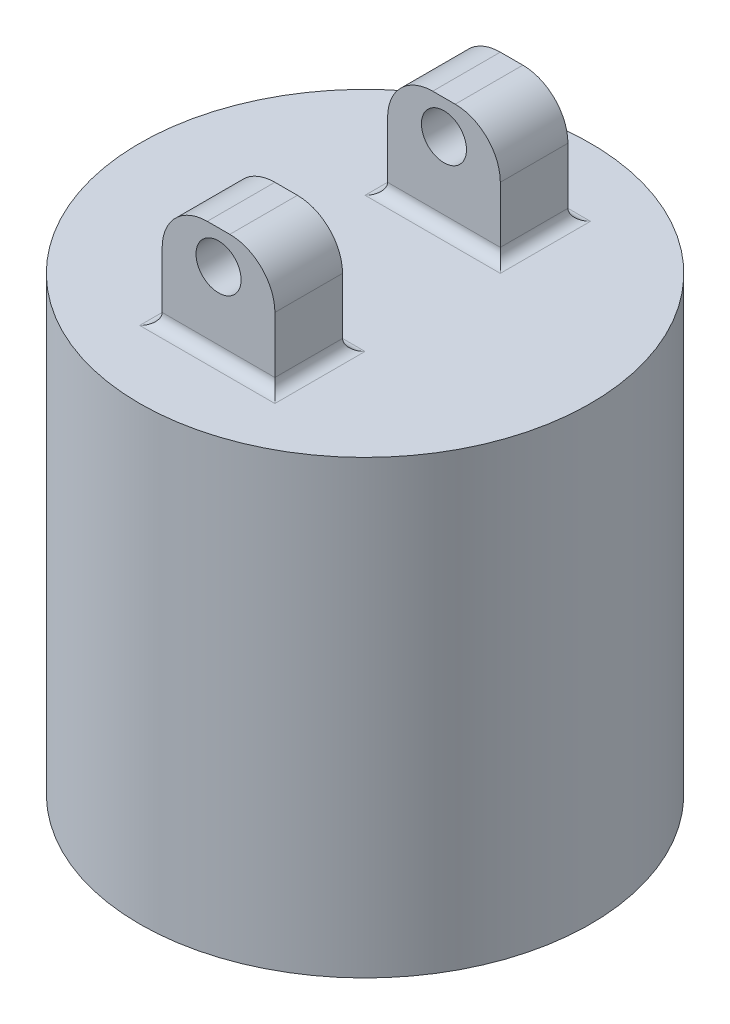
SolidWorks part; units mm, degrees
ref_plane "Front Plane" through (0, 0, 0) normal (0, 0, 1) x (1, 0, 0)
ref_plane "Top Plane" through (0, 0, 0) normal (0, 1, 0) x (1, 0, 0)
ref_plane "Right Plane" through (0, 0, 0) normal (1, 0, 0) x (0, 0, -1)
sketch "Sketch1" plane through (0, 0, 0) normal (0, 1, 0) x (1, 0, 0)
  circle A0 centre (0, 0) radius 50
  dimension "D1" = 100
extrude "Boss-Extrude1" add sketch "Sketch1" along normal blind 100
sketch "Sketch2" plane through (0, 100, 0) normal (0, 1, 0) x (1, 0, 0)
  line L1 (-12.5, -17.5) -> (12.5, -17.5)
  line L2 (-12.5, -17.5) -> (-12.5, -32.5)
  line L3 (-12.5, -32.5) -> (12.5, -32.5)
  line L4 (12.5, -17.5) -> (12.5, -32.5)
  line L5 (-12.5, -17.5) -> (12.5, -32.5) construction
  line L6 (-12.5, -32.5) -> (12.5, -17.5) construction
  point P0 (0, -25)
  point P5 (0, 0)
  point P7 (0, 0)
  point P8 (76.2365, 16.2508)
  dimension "D1" = 25
  dimension "D2" = 0
  dimension "D3" = 25
  dimension "D4" = 15
extrude "Boss-Extrude2" add sketch "Sketch2" along normal blind 25
fillet "Fillet1" radius 2.5 4 edges at (0, 100, 17.5) (-12.5, 100, 25) (0, 100, 32.5) (12.5, 100, 25)
fillet "Fillet2" radius 10 2 edges at (-12.5, 125, 25) (12.5, 125, 25)
sketch "Sketch3" plane through (0, 0, 32.5) normal (0, 0, 1) x (1, 0, 0)
  line L0 (-2.5, 125) -> (2.5, 125) construction
  line L3 (12.5, 115) -> (12.5, 102.5) construction
  circle A0 centre (0, 117.5) radius 5
  point P2 (-9.0351, 108.9927)
  point P5 (0, 125)
  point P6 (-3.9222, 117.5)
  point P10 (-12.5, 111.2644)
  dimension "D1" = 10
  dimension "D2" = 7.5
  dimension "D3" = 12.5
extrude "Cut-Extrude1" cut sketch "Sketch3" against normal blind 25
pattern_circular "CirPattern1" count 2 over 360 about axis through (0, 0, 0) along (0, 1, 0) of "Boss-Extrude2", "Fillet1", "Fillet2", "Cut-Extrude1"
